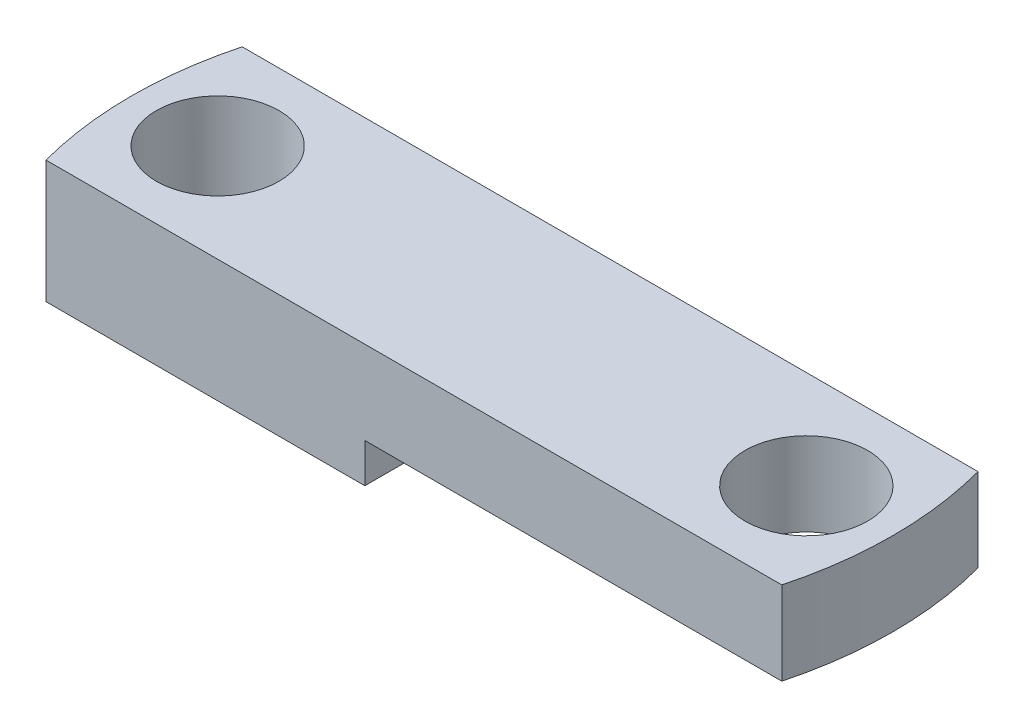
SolidWorks part; units mm, degrees
ref_plane "Front Plane" through (0, 0, 0) normal (0, 0, 1) x (1, 0, 0)
ref_plane "Top Plane" through (0, 0, 0) normal (0, 1, 0) x (1, 0, 0)
ref_plane "Right Plane" through (0, 0, 0) normal (1, 0, 0) x (0, 0, -1)
sketch "Sketch3" plane through (0, 0, 0) normal (0, 1, 0) x (1, 0, 0)
  line L1 (-19.05, 5.08) -> (19.05, 5.08)
  line L3 (-19.05, -5.08) -> (19.05, -5.08)
  line L5 (-19.05, 5.08) -> (19.05, -5.08) construction
  line L6 (-19.05, -5.08) -> (19.05, 5.08) construction
  arc A0 (-19.05, 5.08) -> (-19.05, -5.08) centre (0, 0) ccw
  arc A1 (19.05, -5.08) -> (19.05, 5.08) centre (0, 0) ccw
  point P0 (0, 0)
  dimension "D1" = 10.16
  dimension "D2" = 38.1
extrude "Boss-Extrude2" add sketch "Sketch3" along normal blind 6.35
sketch "Sketch4" plane through (0, 6.35, 0) normal (0, 1, 0) x (1, 0, 0)
  line L0 (-19.7157, 0) -> (19.7157, 0) construction
  line L1 (0, 5.08) -> (0, -5.08) construction
  line L2 (19.05, 5.08) -> (-19.05, 5.08) construction
  line L3 (-19.05, -5.08) -> (19.05, -5.08) construction
  arc A0 (-19.05, 5.08) -> (-19.05, -5.08) centre (0, 0) ccw construction
  arc A1 (19.05, -5.08) -> (19.05, 5.08) centre (0, 0) ccw construction
  circle A6 centre (15.24, 0) radius 3.175
  circle A7 centre (-15.24, 0) radius 3.175
  dimension "D1" = 30.48
  dimension "D5" = 6.35
extrude "Cut-Extrude1" cut sketch "Sketch4" against normal blind 12.7
sketch "Sketch5" plane through (0, 0, 0) normal (0, -1, 0) x (1, 0, 0)
  line L0 (19.05, -5.08) -> (-19.05, -5.08) construction
  line L1 (19.05, 5.08) -> (-2.54, 5.08)
  line L3 (19.05, -5.08) -> (-2.54, -5.08)
  line L4 (-2.54, 5.08) -> (-2.54, -5.08)
  arc A0 (19.05, 5.08) -> (19.05, -5.08) centre (0, 0) cw
  arc A1 (19.05, -5.08) -> (19.05, 5.08) centre (0, 0) ccw construction
  dimension "D1" = 21.59
extrude "Cut-Extrude2" cut sketch "Sketch5" against normal blind 2.032
